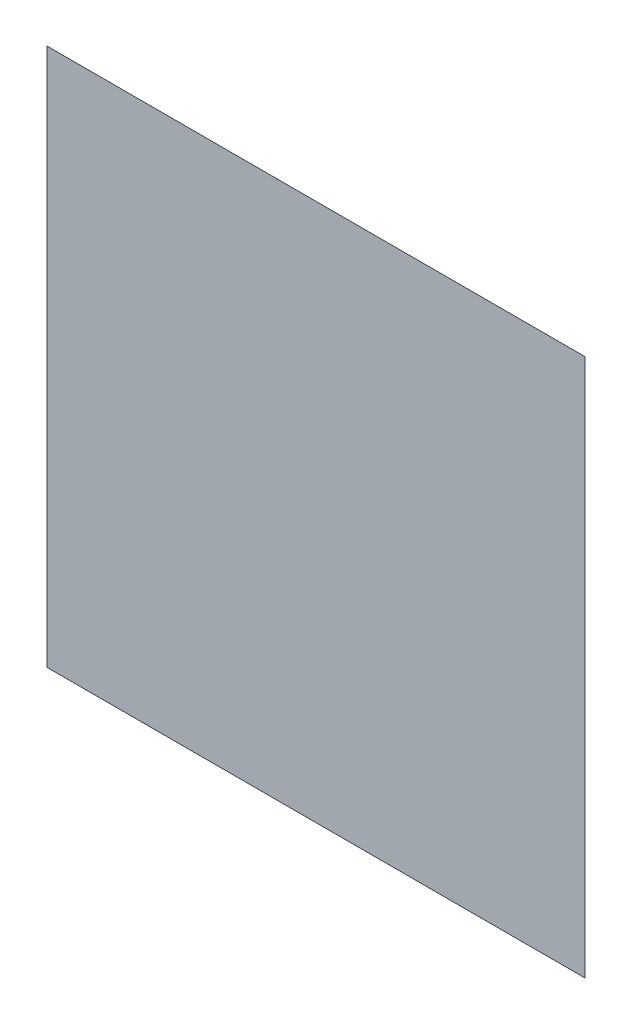
SolidWorks part; units mm, degrees
ref_plane "Front Plane" through (0, 0, 0) normal (0, 0, 1) x (1, 0, 0)
ref_plane "Top Plane" through (0, 0, 0) normal (0, 1, 0) x (1, 0, 0)
ref_plane "Right Plane" through (0, 0, 0) normal (1, 0, 0) x (0, 0, -1)
other "Center of Mass"
sketch "Sketch1" plane through (0, 0, 0) normal (0, 0, 1) x (1, 0, 0)
  line L1 (-454.5455, 393.9394) -> (545.4545, 393.9394)
  line L2 (-454.5455, 393.9394) -> (-454.5455, -606.0606)
  line L3 (-454.5455, -606.0606) -> (545.4545, -606.0606)
  line L4 (545.4545, 393.9394) -> (545.4545, -606.0606)
  dimension "D1" = 1000
  dimension "D2" = 1000
extrude "Boss-Extrude1" add sketch "Sketch1" along normal blind 0.001 contours L2 L1 L4 L3
